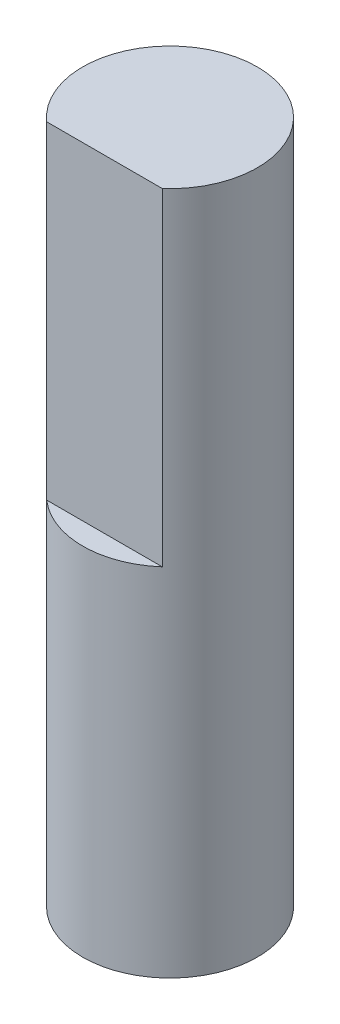
SolidWorks part; units mm, degrees
material "Alloy Steel"
ref_plane "Front Plane" through (0, 0, 0) normal (0, 0, 1) x (1, 0, 0)
ref_plane "Top Plane" through (0, 0, 0) normal (0, 1, 0) x (1, 0, 0)
ref_plane "Right Plane" through (0, 0, 0) normal (1, 0, 0) x (0, 0, -1)
sketch "Sketch1" plane through (0, 0, 0) normal (0, 1, 0) x (1, 0, 0)
  circle A0 centre (0, 0) radius 4
  dimension "D1" = 8
extrude "Boss-Extrude1" add sketch "Sketch1" along normal blind 31.3
sketch "Sketch2" plane through (0, 31.3, 0) normal (0, 1, 0) x (1, 0, 0)
  line L1 (-2.6458, -3) -> (2.6458, -3)
  circle A0 centre (0, 0) radius 4 construction
  arc A1 (-2.6458, -3) -> (2.6458, -3) centre (0, 0) ccw
  point P8 (0, -3)
extrude "Cut-Extrude2" cut sketch "Sketch2" against normal blind 15
